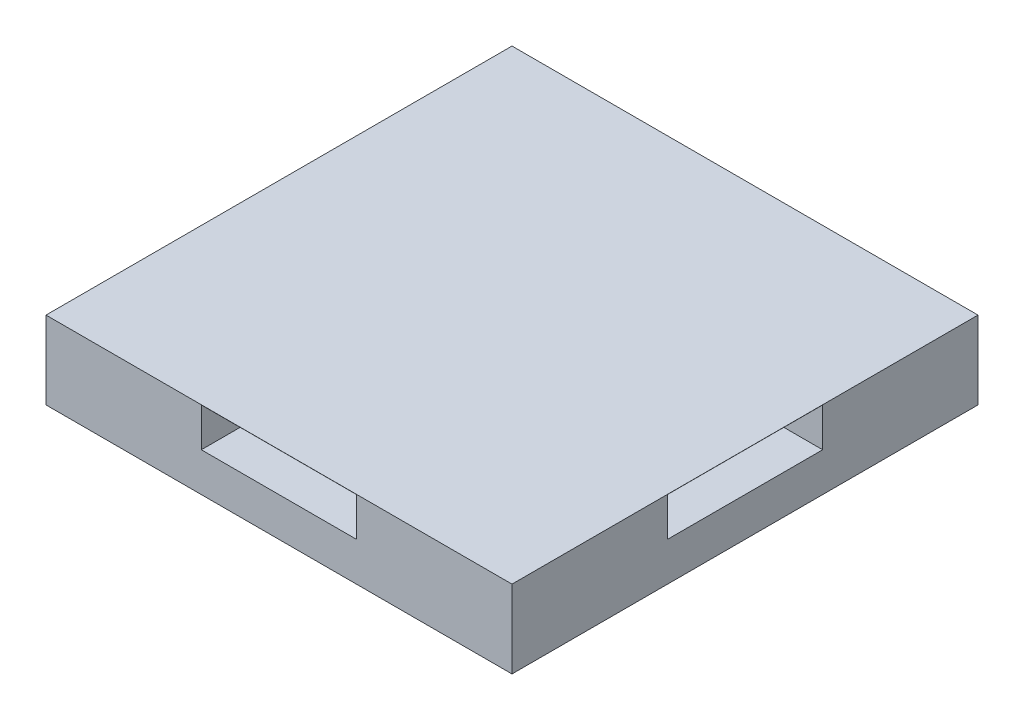
SolidWorks part; units mm, degrees
material "6061 Alloy"
ref_plane "Front Plane" through (0, 0, 0) normal (0, 0, 1) x (1, 0, 0)
ref_plane "Top Plane" through (0, 0, 0) normal (0, 1, 0) x (1, 0, 0)
ref_plane "Right Plane" through (0, 0, 0) normal (1, 0, 0) x (0, 0, -1)
sketch "Sketch1" plane through (0, 0, 0) normal (0, 1, 0) x (1, 0, 0)
  line L1 (0, 0) -> (76.2, 0)
  line L2 (0, 0) -> (0, 76.2)
  line L3 (0, 76.2) -> (76.2, 76.2)
  line L4 (76.2, 0) -> (76.2, 76.2)
  dimension "D1" = 76.2
  dimension "D2" = 76.2
extrude "Boss-Extrude1" add sketch "Sketch1" along normal blind 12.7
sketch "Sketch2" plane through (0, 12.7, 0) normal (0, 1, 0) x (1, 0, 0)
  line L0 (76.2, 76.2) -> (0, 76.2) construction
  line L1 (25.4, 76.2) -> (50.8, 76.2)
  line L2 (25.4, 76.2) -> (25.4, 65.786)
  line L3 (25.4, 65.786) -> (50.8, 65.786)
  line L4 (50.8, 76.2) -> (50.8, 65.786)
  line L5 (0, 76.2) -> (0, 0) construction
  line L6 (0, 50.8) -> (10.414, 50.8)
  line L7 (0, 50.8) -> (0, 25.4)
  line L8 (0, 25.4) -> (10.414, 25.4)
  line L9 (10.414, 50.8) -> (10.414, 25.4)
  line L10 (0, 0) -> (76.2, 0) construction
  line L11 (25.4, 0) -> (50.8, 0)
  line L12 (25.4, 0) -> (25.4, 10.414)
  line L13 (25.4, 10.414) -> (50.8, 10.414)
  line L14 (50.8, 0) -> (50.8, 10.414)
  line L15 (76.2, 0) -> (76.2, 76.2) construction
  line L16 (76.2, 50.8) -> (65.786, 50.8)
  line L17 (76.2, 50.8) -> (76.2, 25.4)
  line L18 (76.2, 25.4) -> (65.786, 25.4)
  line L19 (65.786, 50.8) -> (65.786, 25.4)
  dimension "D1" = 25.4
  dimension "D2" = 25.4
  dimension "D3" = 25.4
  dimension "D4" = 25.4
  dimension "D5" = 25.4
  dimension "D6" = 25.4
  dimension "D7" = 25.4
  dimension "D8" = 25.4
  dimension "D9" = 10.414
  dimension "D10" = 10.414
  dimension "D11" = 10.414
  dimension "D12" = 10.414
extrude "Cut-Extrude1" cut sketch "Sketch2" against normal blind 6.35
sketch "Sketch3" plane through (0, 12.7, 0) normal (0, 1, 0) x (1, 0, 0)
  line L1 (0, 76.2) -> (76.2, 76.2)
  line L2 (0, 76.2) -> (0, 0)
  line L3 (0, 0) -> (76.2, 0)
  line L4 (76.2, 76.2) -> (76.2, 0)
extrude "Boss-Extrude2" add sketch "Sketch3" along normal blind 0.0254
